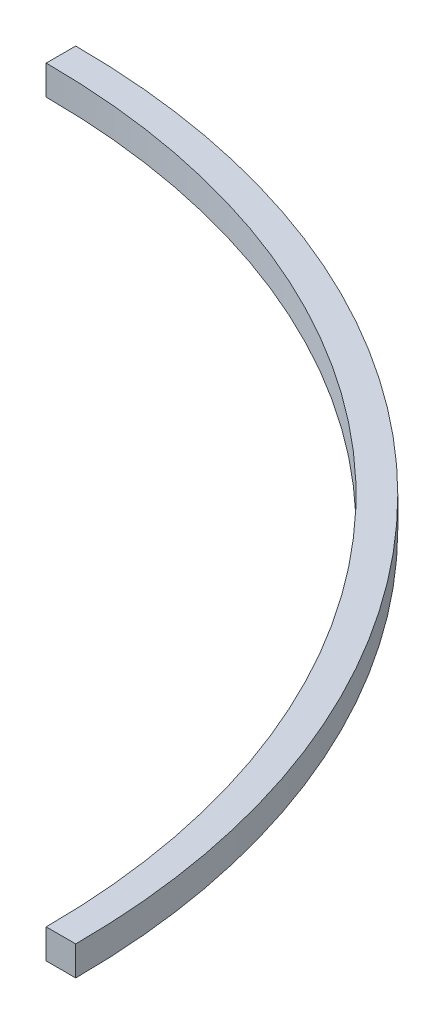
SolidWorks part; units mm, degrees
ref_plane "Front Plane" through (0, 0, 0) normal (0, 0, 1) x (1, 0, 0)
ref_plane "Top Plane" through (0, 0, 0) normal (0, 1, 0) x (1, 0, 0)
ref_plane "Right Plane" through (0, 0, 0) normal (1, 0, 0) x (0, 0, -1)
sketch "Sketch1" plane through (0, 0, 0) normal (0, 1, 0) x (1, 0, 0)
  line L0 (0, 79) -> (0, 76)
  line L1 (76, 0) -> (79, 0)
  arc A0 (0, 76) -> (76, 0) centre (0, 0) cw
  arc A1 (0, 79) -> (79, 0) centre (0, 0) cw
  dimension "D1" = 79
  dimension "D2" = 76
extrude "Boss-Extrude1" add sketch "Sketch1" along normal blind 3
